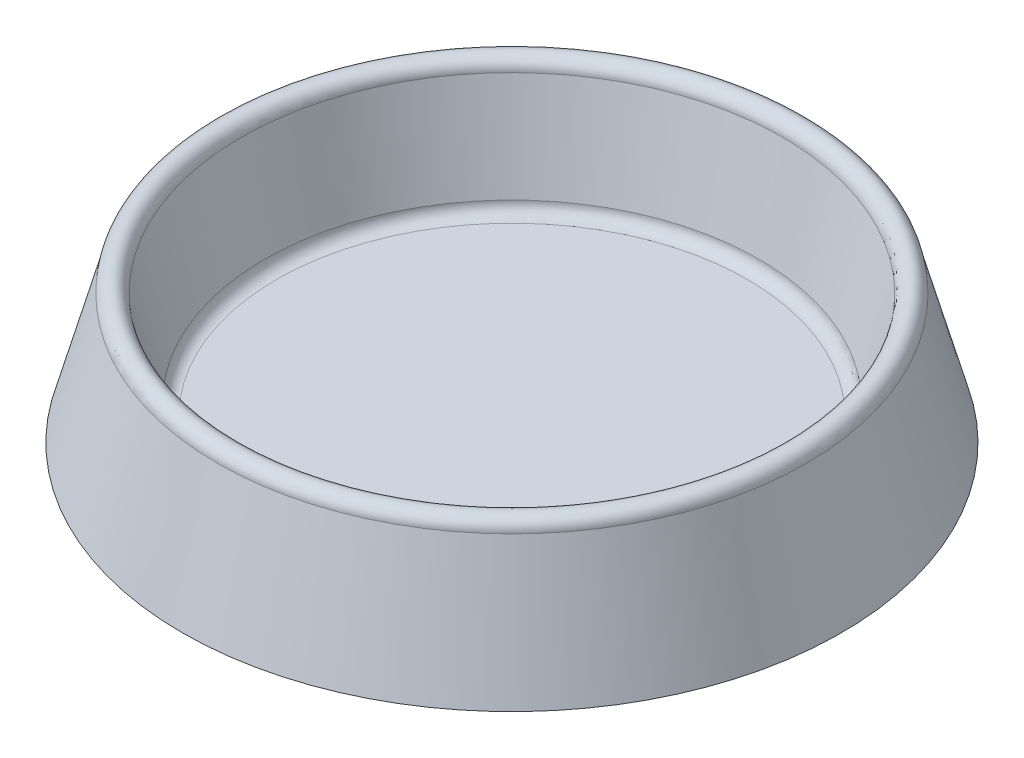
SolidWorks part; units mm, degrees
ref_plane "Front Plane" through (0, 0, 0) normal (0, 0, 1) x (1, 0, 0)
ref_plane "Top Plane" through (0, 0, 0) normal (0, 1, 0) x (1, 0, 0)
ref_plane "Right Plane" through (0, 0, 0) normal (1, 0, 0) x (0, 0, -1)
sketch "Sketch1" plane through (0, 0, 0) normal (0, 0, 1) x (1, 0, 0)
  line L0 (0, 41.8447) -> (0, -33.1068) construction
  line L1 (-70, 4.3689) -> (0, 4.3689)
  line L2 (-62.5, 31.7476) -> (-70, 4.3689)
  line L3 (-57.5, 31.7476) -> (-52.5, 11.8689)
  line L4 (-50, 9.3689) -> (0, 9.3689)
  line L5 (0, 4.3689) -> (0, 9.3689)
  arc A0 (-57.5, 31.7476) -> (-62.5, 31.7476) centre (-60, 31.7476) ccw
  arc A1 (-52.5, 11.8689) -> (-50, 9.3689) centre (-50, 11.8689) ccw
  point P16 (0, 4.3689)
  dimension "D1" = 70
  dimension "D3" = 5
  dimension "D4" = 5
  dimension "D2" = 5
  dimension "D5" = 10
  dimension "D6" = 10
revolve "Revolve1" add sketch "Sketch1" angle 360 about L0
